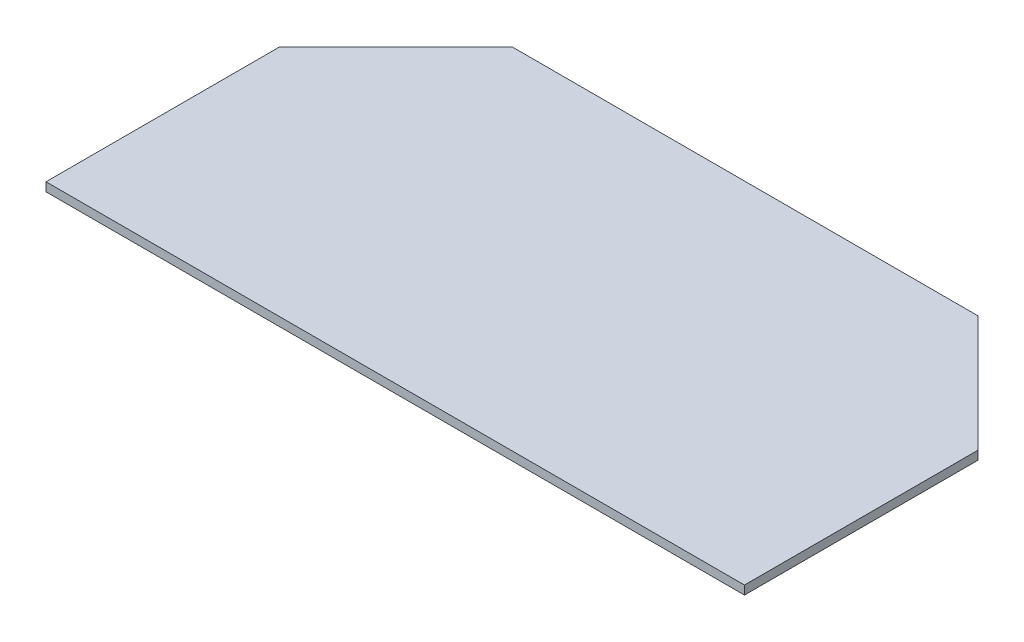
SolidWorks part; units mm, degrees
material "ｶﾞﾗｽ"
ref_plane "Front Plane" through (0, 0, 0) normal (0, 0, 1) x (1, 0, 0)
ref_plane "Top Plane" through (0, 0, 0) normal (0, 1, 0) x (1, 0, 0)
ref_plane "Right Plane" through (0, 0, 0) normal (1, 0, 0) x (0, 0, -1)
sketch "Sketch1" plane through (0, 0, 0) normal (0, 1, 0) x (1, 0, 0)
  line L0 (-39.6921, 30.3169) -> (13.7579, 30.3169)
  line L1 (13.7579, 30.3169) -> (27.1079, 16.9669)
  line L2 (27.1079, 16.9669) -> (27.1079, -9.8331)
  line L3 (27.1079, -9.8331) -> (-53.0421, -9.8331)
  line L4 (-53.0421, -9.8331) -> (-53.0421, 16.9669)
  line L5 (-53.0421, 16.9669) -> (-39.6921, 30.3169)
  dimension "D1" = 80.15
  dimension "D2" = 26.8
  dimension "D3" = 26.8
  dimension "D4" = 13.35
  dimension "D5" = 13.35
  dimension "D6" = 40.15
extrude "Boss-Extrude1" add sketch "Sketch1" along normal blind 1
